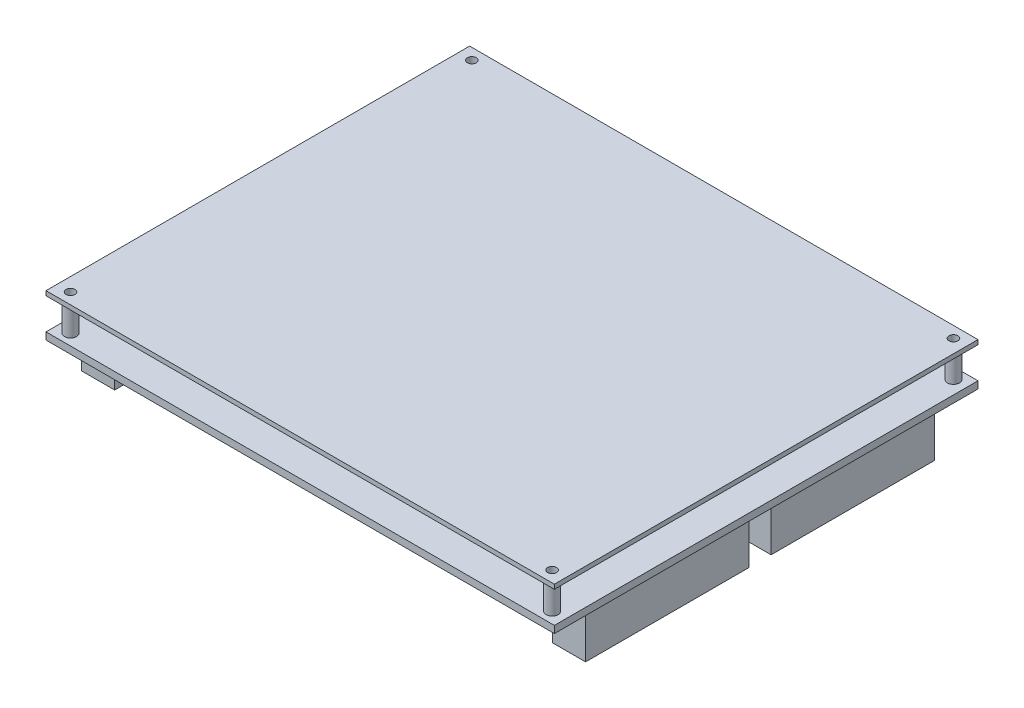
SolidWorks part; units mm, degrees
ref_plane "Front Plane" through (0, 0, 0) normal (0, 0, 1) x (1, 0, 0)
ref_plane "Top Plane" through (0, 0, 0) normal (0, 1, 0) x (1, 0, 0)
ref_plane "Right Plane" through (0, 0, 0) normal (1, 0, 0) x (0, 0, -1)
sketch "Sketch3" plane through (0, 0, 0) normal (0, 1, 0) x (1, 0, 0)
  line L1 (-57, 47.5) -> (57, 47.5)
  line L2 (-57, 47.5) -> (-57, -47.5)
  line L3 (-57, -47.5) -> (57, -47.5)
  line L4 (57, 47.5) -> (57, -47.5)
  dimension "D1" = 114
  dimension "D2" = 95
  dimension "D3" = 57
  dimension "D4" = 47.5
extrude "Extrude1" add sketch "Sketch3" along normal blind 1.6
sketch "Sketch4" plane through (0, 0, 0) normal (0, -1, 0) x (1, 0, 0)
  line L0 (57, -47.5) -> (-57, -47.5) construction
  line L1 (-56.5, 40) -> (-49.1, 40)
  line L2 (-56.5, 40) -> (-56.5, 3.4)
  line L3 (-56.5, 3.4) -> (-49.1, 3.4)
  line L4 (-49.1, 40) -> (-49.1, 3.4)
  line L5 (-56.5, -5.8) -> (-49.1, -5.8)
  line L6 (-56.5, -5.8) -> (-56.5, -42.4)
  line L7 (-56.5, -42.4) -> (-49.1, -42.4)
  line L8 (-49.1, -5.8) -> (-49.1, -42.4)
  line L9 (49.1, 40) -> (56.5, 40)
  line L10 (49.1, 40) -> (49.1, 3.4)
  line L11 (49.1, 3.4) -> (56.5, 3.4)
  line L12 (56.5, 40) -> (56.5, 3.4)
  line L13 (49.1, -1.6) -> (56.5, -1.6)
  line L14 (49.1, -1.6) -> (49.1, -38.2)
  line L15 (49.1, -38.2) -> (56.5, -38.2)
  line L16 (56.5, -1.6) -> (56.5, -38.2)
  line L17 (-57, -47.5) -> (-57, 47.5) construction
  line L18 (57, 47.5) -> (57, -47.5) construction
  dimension "D1" = 36.6
  dimension "D2" = 7.4
  dimension "D3" = 5.1
  dimension "D4" = 9.3
  dimension "D5" = 50.9
  dimension "D6" = 50.9
  dimension "D7" = 0.5
  dimension "D8" = 0.5
extrude "Extrude2" add sketch "Sketch4" along normal blind 9.5
sketch "Sketch5" plane through (0, 1.6, 0) normal (0, 1, 0) x (-1, 0, 0)
  line L1 (57, -47.5) -> (57, 47.5) construction
  line L2 (-57, 47.5) -> (-57, -47.5) construction
  line L3 (57, 47.5) -> (-57, 47.5) construction
  line L4 (-57, -47.5) -> (57, -47.5) construction
  circle A0 centre (54, -45) radius 1.35
  circle A1 centre (54, 45) radius 1.35
  circle A2 centre (-54, 45) radius 1.35
  circle A3 centre (-54, -45) radius 1.35
  dimension "D1" = 3
  dimension "D2" = 3
  dimension "D3" = 3
  dimension "D4" = 2.5
  dimension "D5" = 2.5
extrude "Extrude3" add sketch "Sketch5" along normal blind 7
sketch "Sketch7" plane through (0, 8.6, 0) normal (0, 1, 0) x (-1, 0, 0)
  line L1 (57, -47.5) -> (-57, -47.5)
  line L2 (57, -47.5) -> (57, 47.5)
  line L3 (57, 47.5) -> (-57, 47.5)
  line L4 (-57, -47.5) -> (-57, 47.5)
extrude "Extrude4" add sketch "Sketch7" along normal blind 1
sketch "Sketch8" plane through (0, 9.6, 0) normal (0, 1, 0) x (-1, 0, 0)
  circle A0 centre (54, -45) radius 1
  circle A1 centre (54, 45) radius 1
  circle A2 centre (-54, 45) radius 1
  circle A3 centre (-54, -45) radius 1
  circle A4 centre (54, -45) radius 1.35 construction
  circle A5 centre (54, 45) radius 1.35 construction
  circle A6 centre (-54, 45) radius 1.35 construction
  circle A7 centre (-54, -45) radius 1.35 construction
  dimension "D1" = 2
extrude "Cut-Extrude1" cut sketch "Sketch8" against normal through all
